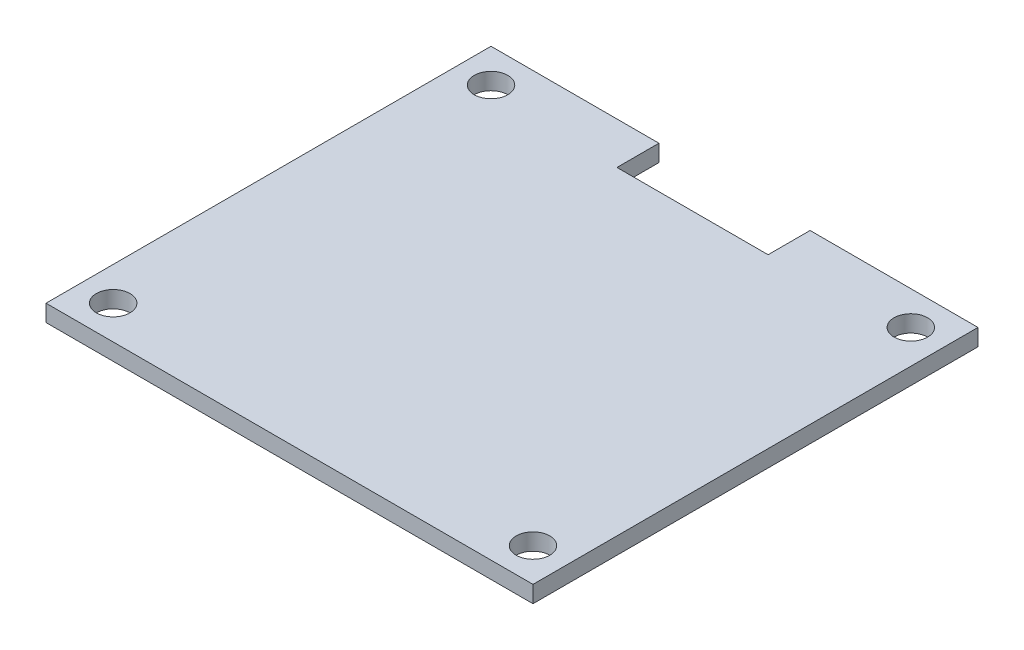
SolidWorks part; units mm, degrees
ref_plane "Front Plane" through (0, 0, 0) normal (0, 0, 1) x (1, 0, 0)
ref_plane "Top Plane" through (0, 0, 0) normal (0, 1, 0) x (1, 0, 0)
ref_plane "Right Plane" through (0, 0, 0) normal (1, 0, 0) x (0, 0, -1)
sketch "Sketch1" plane through (0, 0, 0) normal (0, 1, 0) x (1, 0, 0)
  line L1 (-29, 26.5) -> (29, 26.5)
  line L2 (-29, 26.5) -> (-29, -26.5)
  line L3 (-29, -26.5) -> (29, -26.5)
  line L4 (29, 26.5) -> (29, -26.5)
  line L5 (-29, 26.5) -> (29, -26.5) construction
  line L6 (-29, -26.5) -> (29, 26.5) construction
  point P0 (0, 0)
  dimension "D1" = 58
  dimension "D2" = 53
extrude "Boss-Extrude1" add sketch "Sketch1" along normal blind 2
hole_wizard "Ø4.0mm Dowel Hole1" positions "Sketch2" profile "Sketch3" hole size "Ø4.0" standard "ANSI Metric" end condition up to next
sketch "Sketch2" plane through (0, 2, 0) normal (0, 1, 0) x (1, 0, 0)
  line L0 (29, 26.5) -> (-29, 26.5) construction
  line L1 (29, -26.5) -> (29, 26.5) construction
  line L2 (-29, 26.5) -> (-29, -26.5) construction
  line L3 (-29, -26.5) -> (29, -26.5) construction
  point P0 (25, 22.5)
  point P2 (-25, 22.5)
  point P4 (-25, -22.5)
  point P6 (25, -22.5)
  dimension "D1" = 4
  dimension "D2" = 4
  dimension "D3" = 4
  dimension "D4" = 4
  dimension "D5" = 4
  dimension "D6" = 4
  dimension "D7" = 4
  dimension "D8" = 4
sketch "Sketch3" plane through (25, 2, -22.5) normal (1, 0, 0) x (0, 0, 1)
  line L0 (0, 0) -> (0, 2)
  line L1 (0, 2) -> (2, 2)
  line L2 (2, 2) -> (2, 0)
  line L5 (2, 0) -> (0, 0)
  line L11 (0, -6.35) -> (0, 107.95) construction
  dimension "Thru Hole Dia." = 4
  dimension "Thru Hole Depth" = 2
sketch "Sketch4" plane through (0, 2, 0) normal (0, 1, 0) x (1, 0, 0)
  line L0 (29, 26.5) -> (-29, 26.5) construction
  line L1 (-9, 26.5) -> (9, 26.5)
  line L2 (-9, 26.5) -> (-9, 21.5)
  line L3 (-9, 21.5) -> (9, 21.5)
  line L4 (9, 26.5) -> (9, 21.5)
  point P6 (0, 26.5)
  point P7 (0, 26.5)
  dimension "D1" = 5
  dimension "D2" = 18
extrude "Cut-Extrude1" cut sketch "Sketch4" against normal up to surface (2 mm away) up to face at (25, 0, -20.5)
